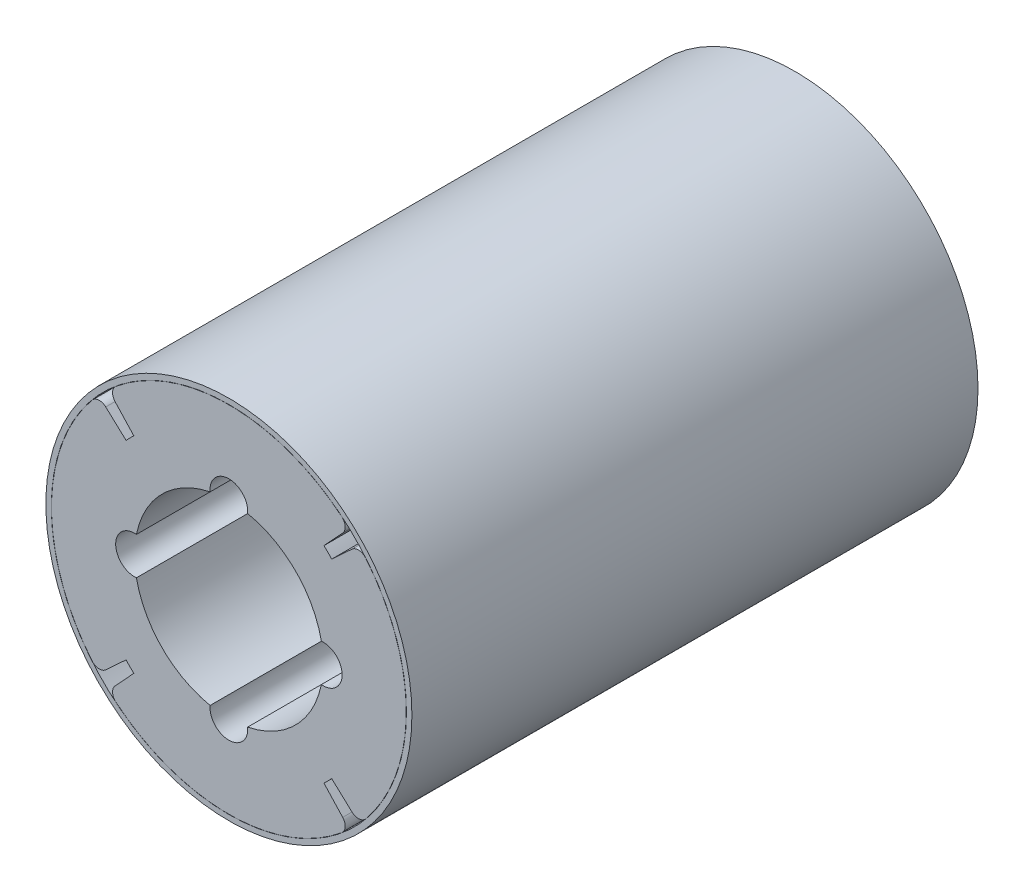
SolidWorks part; units mm, degrees
ref_plane "Front Plane" through (0, 0, 0) normal (0, 0, 1) x (1, 0, 0)
ref_plane "Top Plane" through (0, 0, 0) normal (0, 1, 0) x (1, 0, 0)
ref_plane "Right Plane" through (0, 0, 0) normal (1, 0, 0) x (0, 0, -1)
sketch "Sketch1" plane through (0, 0, 0) normal (0, 0, 1) x (1, 0, 0)
  circle A2 centre (0, 0) radius 5
  circle A3 centre (0, 0) radius 7.42
  dimension "D1" = 10
  dimension "D2" = 14.84
extrude "Boss-Extrude1" add sketch "Sketch1" along normal blind 30
sketch "Sketch2" plane through (0, 0, 0) normal (0, 0, 1) x (1, 0, 0)
  line L0 (0, 0) -> (0, 9.4) construction
  line L2 (5.0367, 5.4487) -> (6.0318, 6.5251)
  line L3 (-5.0367, 5.4487) -> (-6.0318, 6.5251)
  arc A0 (-5.9829, 7.2502) -> (5.9829, 7.2502) centre (0, 0) cw
  arc A1 (-5.0367, 5.4487) -> (5.0367, 5.4487) centre (0, 0) cw
  arc A2 (6.0318, 6.5251) -> (5.9829, 7.2502) centre (5.6646, 6.8645) ccw
  arc A3 (-6.0318, 6.5251) -> (-5.9829, 7.2502) centre (-5.6646, 6.8645) cw
  point P14 (6.3807, 6.9026)
  point P17 (-6.3807, 6.9026)
  dimension "D4" = 0.5
  dimension "D2" = 7.42
  dimension "D1" = 85.5
  dimension "D3" = 1.98
extrude "Boss-Extrude2" add sketch "Sketch2" along normal blind 30
pattern_circular "CirPattern1" count 4 over 360 about axis through (0, 0, 0) along (0, 0, 1) of "Boss-Extrude2"
sketch "Sketch3" plane through (0, 0, 0) normal (0, 0, 1) x (1, 0, 0)
  circle A0 centre (0, 0) radius 9.41
  circle A1 centre (0, 0) radius 9.7
  dimension "D1" = 19.4
extrude "Boss-Extrude3" add sketch "Sketch3" along normal blind 30 separate body
sketch "Sketch4" plane through (0, 0, 0) normal (0, 0, 1) x (1, 0, 0)
  line L0 (0, 5) -> (0, 0) construction
  circle A0 centre (0, 5) radius 1
  dimension "D2" = 2
  dimension "D1" = 5
extrude "Cut-Extrude2" cut sketch "Sketch4" along normal blind 30
pattern_circular "CirPattern2" count 4 over 360 about axis through (0, 0, 0) along (0, 0, 1) of "Cut-Extrude2"
equation "\"OuterDiam\"= 19.4"
equation "\"InnerDiam\"= 10"
equation "\"PolePairs\"= 2"
equation "\"tMagnet\"= 1.98"
equation "\"Length\"= 30"
equation "\"tSleeve\"= 0.3"
equation "\"D1@Sketch1\"=\"InnerDiam\""
equation "\"D2@Sketch1\"=\"OuterDiam\"-2*(\"tMagnet\"+\"tSleeve\")"
equation "\"D1@Boss-Extrude1\"=\"Length\""
equation "\"D3@Sketch2\"=\"tMagnet\""
equation "\"tauP\"= 0.95"
equation "\"D1@Sketch2\"=360deg/(2*\"PolePairs\")*\"tauP\""
equation "\"D1@Boss-Extrude2\"=\"Length\""
equation "\"D1@CirPattern1\"=2*\"PolePairs\""
equation "\"D1@Sketch3\"=\"OuterDiam\""
equation "\"D2@Sketch3\"=\"tSleeve\"-0.01mm"
equation "\"D1@Boss-Extrude3\"=\"Length\""
equation "\"D1@Sketch4\"=\"InnerDiam\"/2"
equation "\"D1@Cut-Extrude2\"=\"Length\""
equation "\"D2@Sketch2\"=\"OuterDiam\"/2-(\"tMagnet\"+\"tSleeve\")"
